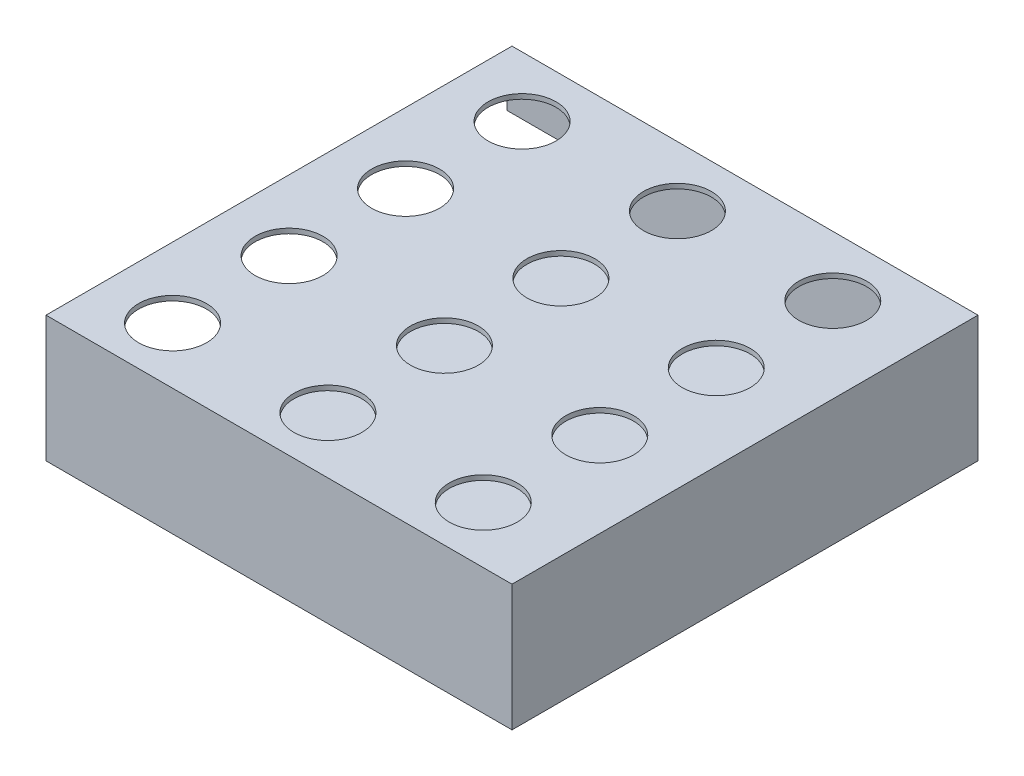
SolidWorks part; units mm, degrees
ref_plane "Front Plane" through (0, 0, 0) normal (0, 0, 1) x (1, 0, 0)
ref_plane "Top Plane" through (0, 0, 0) normal (0, 1, 0) x (1, 0, 0)
ref_plane "Right Plane" through (0, 0, 0) normal (1, 0, 0) x (0, 0, -1)
sketch "Sketch1" plane through (0, 0, 0) normal (0, 0, 1) x (1, 0, 0)
  line L1 (-304.8, -82.55) -> (304.8, -82.55)
  line L2 (-304.8, -82.55) -> (-304.8, 82.55)
  line L3 (-304.8, 82.55) -> (304.8, 82.55)
  line L4 (304.8, -82.55) -> (304.8, 82.55)
  line L5 (-304.8, -82.55) -> (304.8, 82.55) construction
  line L6 (-304.8, 82.55) -> (304.8, -82.55) construction
  point P0 (0, 0)
  dimension "D1" = 165.1
  dimension "D2" = 609.6
extrude "Boss-Extrude1" add sketch "Sketch1" against normal blind 609.6
sketch "Sketch2" plane through (0, 82.55, 0) normal (0, 1, 0) x (1, 0, 0)
  line L0 (-212.9415, 609.6) -> (-212.9415, 0) construction
  line L1 (-304.8, 609.6) -> (304.8, 609.6)
  line L2 (-304.8, 609.6) -> (-304.8, 0)
  line L3 (-304.8, 0) -> (304.8, 0)
  line L4 (304.8, 609.6) -> (304.8, 0)
  circle A0 centre (-212.9415, 378.5282) radius 44.45
  circle A1 centre (-212.9415, 226.1282) radius 44.45
  circle A2 centre (-212.9415, 73.7282) radius 44.45
  circle A3 centre (-9.7415, 226.1282) radius 44.45
  circle A4 centre (-9.7415, 378.5282) radius 44.45
  circle A5 centre (-9.7415, 73.7282) radius 44.45
  circle A6 centre (193.4585, 226.1282) radius 44.45
  circle A7 centre (193.4585, 378.5282) radius 44.45
  circle A8 centre (193.4585, 73.7282) radius 44.45
  circle A9 centre (-212.9415, 530.9282) radius 44.45
  circle A10 centre (-9.7415, 530.9282) radius 44.45
  circle A11 centre (193.4585, 530.9282) radius 44.45
  dimension "D1" = 88.9
  dimension "D2" = 3
  dimension "D3" = 3
  dimension "D4" = 2
shell "Shell1" thickness 6.35
extrude "Cut-Extrude2" cut sketch "Sketch2" against normal blind 7.62 contours A9 L0 | L0 A9 | A10 | A11 | A2 | A0 | A4 | A3 | A1 | A5 | A8 | A6 | A7
sketch "Sketch4" plane through (0, 0, -609.6) normal (0, 0, -1) x (-1, 0, 0)
  line L5 (304.8, -76.2) -> (215.9, -76.2)
  line L6 (304.8, -76.2) -> (304.8, 12.7)
  line L7 (304.8, 12.7) -> (215.9, 12.7)
  line L8 (215.9, -76.2) -> (215.9, 12.7)
  dimension "D1" = 88.9
  dimension "D2" = 88.9
extrude "Cut-Extrude3" cut sketch "Sketch4" against normal blind 7.62
